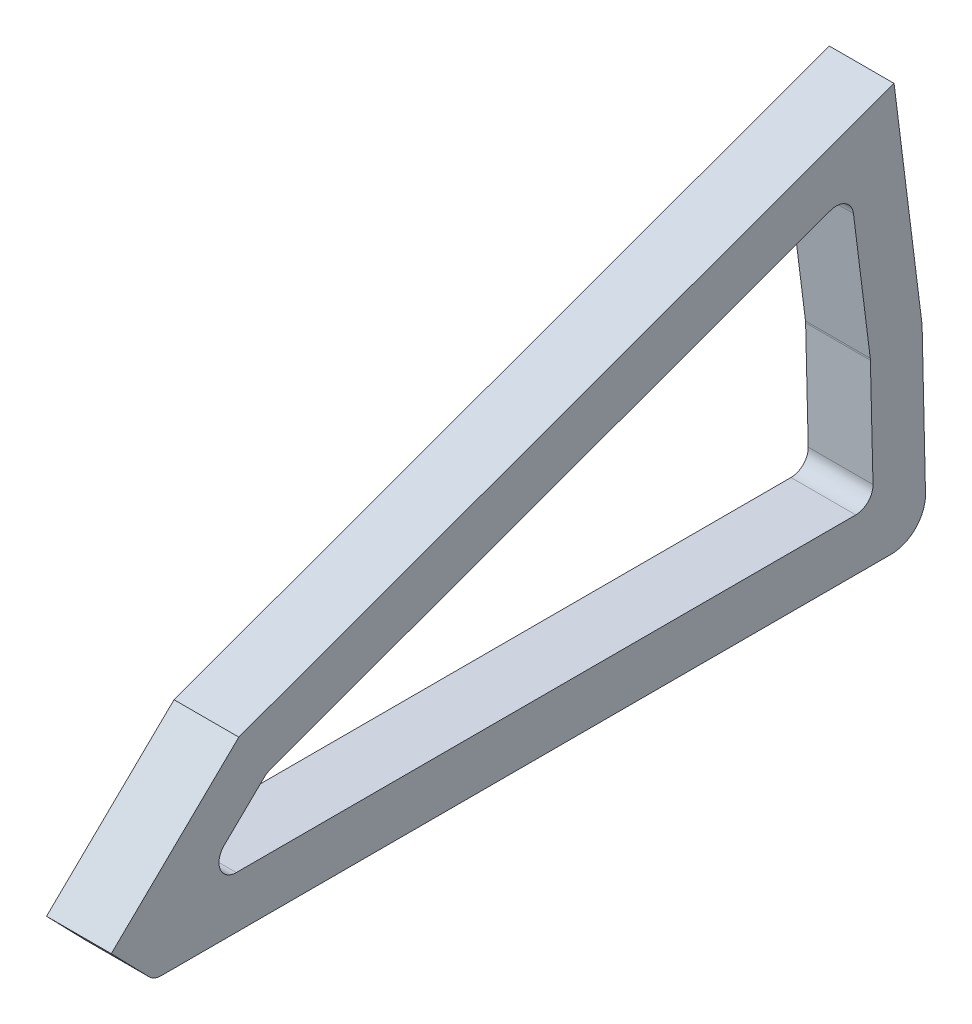
SolidWorks part; units mm, degrees
ref_plane "Front Plane" through (0, 0, 0) normal (0, 0, 1) x (1, 0, 0)
ref_plane "Top Plane" through (0, 0, 0) normal (0, 1, 0) x (1, 0, 0)
ref_plane "Right Plane" through (0, 0, 0) normal (1, 0, 0) x (0, 0, -1)
sketch "Sketch1" plane through (0, 0, 0) normal (1, 0, 0) x (0, 0, -1)
  line L0 (-80.7644, 24.012) -> (70.9853, 79.2444)
  line L11 (70.262, -14.8585) -> (-98.6996, -14.8585)
  line L13 (70.9853, 79.2444) -> (77.4757, 27.5552)
  line L14 (-73.4445, 13.9061) -> (56.2409, 61.1077)
  line L15 (61.5778, 57.8473) -> (65.4686, 26.8615)
  line L16 (66.105, 1.2377) -> (65.4986, 26.4593)
  line L18 (77.4757, 27.5552) -> (78.2599, -6.6753)
  line L19 (62.1062, -2.8585) -> (-81.3554, -2.8585)
  line L20 (-80.7644, 24.012) -> (-110.2977, -4.6519)
  line L22 (-74.8623, 13.0177) -> (-84.1413, 4.0119)
  line L28 (-110.2977, -4.6519) -> (-100.3916, -14.8585) construction
  line L29 (78.4473, -14.8585) -> (-100.3916, -14.8585) construction
  line L31 (-110.2977, -4.6519) -> (-101.57, -13.6444)
  line L33 (-74.2484, 13.6135) -> (60.953, 62.8228) construction
  line L34 (-74.2484, 13.6135) -> (-91.2201, -2.8585) construction
  line L35 (60.953, 62.8228) -> (65.4938, 26.6612) construction
  line L36 (66.2035, -2.8585) -> (65.4938, 26.6612) construction
  line L37 (66.2035, -2.8585) -> (-91.2201, -2.8585) construction
  line L38 (66.2035, -2.8585) -> (66.2035, -2.8585) construction
  line L39 (-91.2201, -2.8585) -> (-91.2201, -2.8585) construction
  line L40 (78.4473, -12.8563) -> (78.4473, -14.8585) construction
  line L41 (78.4473, -12.8563) -> (77.4757, 27.5552) construction
  arc A0 (-101.57, -13.6444) -> (-98.6996, -14.8585) centre (-98.6996, -10.8585) ccw
  arc A1 (-73.4445, 13.9061) -> (-74.8623, 13.0177) centre (-72.0765, 10.1473) ccw
  arc A2 (56.2409, 61.1077) -> (61.5778, 57.8473) centre (57.609, 57.349) cw
  arc A3 (65.4986, 26.4593) -> (65.4686, 26.8615) centre (61.4998, 26.3632) ccw
  arc A4 (62.1062, -2.8585) -> (66.105, 1.2377) centre (62.1062, 1.1415) ccw
  arc A5 (-81.3554, -2.8585) -> (-84.1413, 4.0119) centre (-81.3554, 1.1415) cw
  arc A6 (78.2599, -6.6753) -> (70.262, -14.8585) centre (70.262, -6.8585) cw
  dimension "D2" = 4
  dimension "D3" = 4
  dimension "D4" = 8
  dimension "D1" = 12
extrude "Boss-Extrude1" add sketch "Sketch1" along normal blind 15
